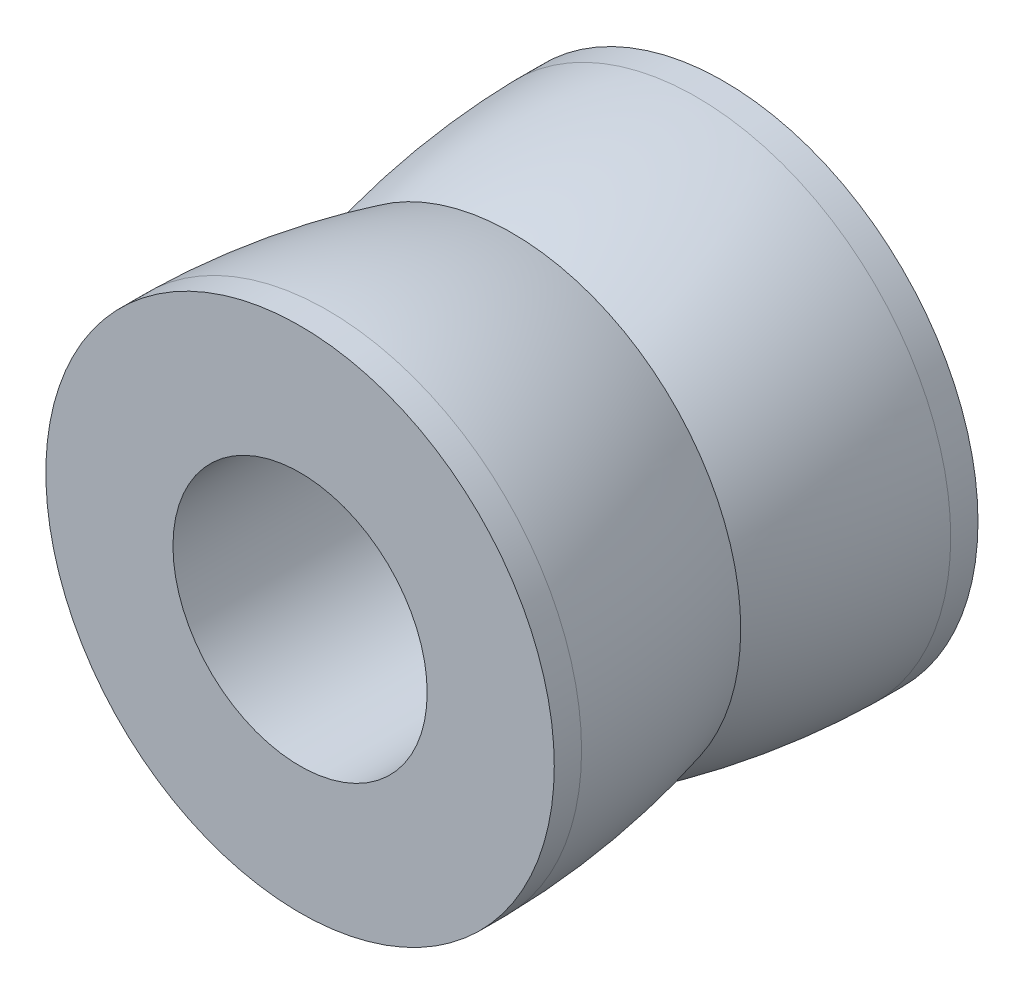
SolidWorks part; units mm, degrees
material "AISI Tip 316L paslanmaz çelik"
ref_plane "Ön Düzlem" through (0, 0, 0) normal (0, 0, 1) x (1, 0, 0)
ref_plane "Üst Düzlem" through (0, 0, 0) normal (0, 1, 0) x (1, 0, 0)
ref_plane "Sağ Düzlem" through (0, 0, 0) normal (1, 0, 0) x (0, 0, -1)
sketch "Çizim1" plane through (0, 0, 0) normal (0, 0, 1) x (1, 0, 0)
  circle A0 centre (0, 0) radius 6
  circle A1 centre (0, 0) radius 3
  dimension "D1" = 12
  dimension "D2" = 6
extrude "Yükseklik-Ekstrüzyon1" add sketch "Çizim1" along normal blind 10
sketch "Çizim2" plane through (0, 0, 0) normal (0, 1, 0) x (1, 0, 0)
  line L3 (-6, 0) -> (-6, -10)
  arc A0 (-6, -10) -> (-5.4, -5) centre (12.45, -9.678) cw
  arc A1 (-6, 0) -> (-5.4, -5) centre (12.45, -0.322) ccw
ref_axis "Eksen1" through (0, 0, 10) along (0, 0, -1)
revolve "Kes-Döndür1" cut sketch "Çizim2" angle 360 about axis through (0, 0, 10) along (0, 0, -1)
